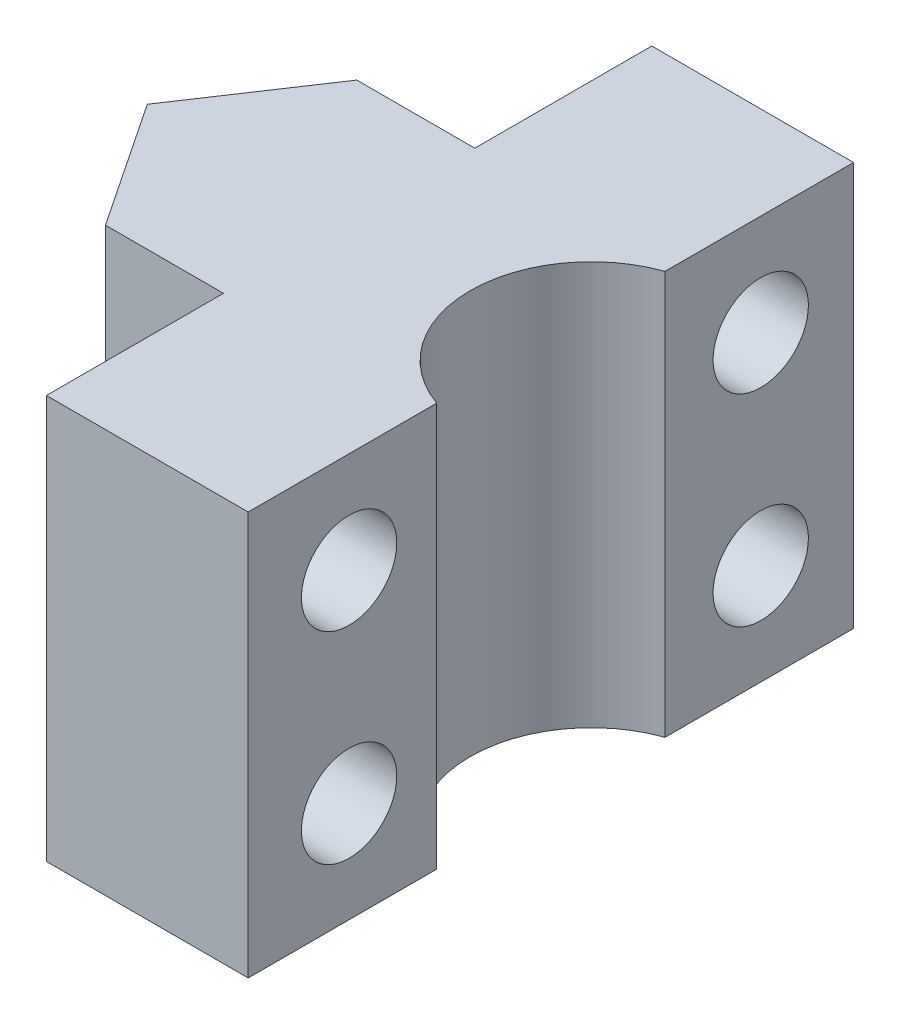
SolidWorks part; units mm, degrees
ref_plane "Front Plane" through (0, 0, 0) normal (0, 0, 1) x (1, 0, 0)
ref_plane "Top Plane" through (0, 0, 0) normal (0, 1, 0) x (1, 0, 0)
ref_plane "Right Plane" through (0, 0, 0) normal (1, 0, 0) x (0, 0, -1)
sketch "Sketch1" plane through (0, 0, 0) normal (0, 1, 0) x (1, 0, 0)
  line L1 (0, 0) -> (12.7, 0)
  line L2 (0, 0) -> (0, 19.05)
  line L3 (0, 19.05) -> (12.7, 19.05)
  line L4 (12.7, 0) -> (12.7, 19.05)
  dimension "D1" = 12.7
  dimension "D2" = 19.05
extrude "Boss-Extrude1" add sketch "Sketch1" along normal blind 12.7
sketch "Sketch4" plane through (0, 12.7, 0) normal (0, 1, 0) x (1, 0, 0)
  line L0 (0, 9.525) -> (6.35, 19.05)
  line L1 (0, 19.05) -> (0, 0) construction
  line L2 (12.7, 19.05) -> (0, 19.05) construction
  line L3 (6.35, 19.05) -> (0, 19.05)
  line L4 (0, 19.05) -> (0, 0)
  line L5 (0, 0) -> (6.35, 0)
  line L6 (0, 0) -> (12.7, 0) construction
  line L7 (6.35, 0) -> (0, 9.525)
  line L8 (12.7, 0) -> (12.7, 19.05) construction
  circle A0 centre (13.97, 9.525) radius 3.81
  line M1 (0, 19.05) -> (0, 0)
  line M2 (0, 0) -> (12.7, 0)
  line M3 (12.7, 0) -> (12.7, 19.05)
  line M4 (12.7, 19.05) -> (0, 19.05)
  dimension "D1" = 7.62
  dimension "D2" = 1.27
extrude "Cut-Extrude2" cut sketch "Sketch4" against normal blind 12.7 contours L0 M1 M4 | L7 M2 M1 | A0 M3
sketch "Sketch5" plane through (12.7, 0, 0) normal (1, 0, 0) x (0, 0, -1)
  line L0 (0, 12.7) -> (5.9329, 12.7) construction
  line L1 (0, 12.7) -> (0, 0) construction
  circle A0 centre (3.175, 9.525) radius 1.5
  circle A1 centre (16.129, 9.525) radius 1.5
  circle A2 centre (16.129, 3.175) radius 1.5
  circle A3 centre (3.175, 3.175) radius 1.5
  dimension "D1" = 3
  dimension "D2" = 3.175
  dimension "D3" = 3.175
  dimension "D4" = 2
  dimension "D5" = 2
extrude "Cut-Extrude3" cut sketch "Sketch5" against normal blind 12.7
sketch "Sketch6" plane through (0, 0, 0) normal (0, -1, 0) x (1, 0, 0)
  line L0 (6.35, 0) -> (6.35, -5.5703)
  line L2 (2.6365, -5.5703) -> (6.35, 0)
  line L3 (2.6365, -5.5703) -> (6.35, -5.5703)
  line L4 (6.35, 0) -> (0, -9.525) construction
extrude "Cut-Extrude4" cut sketch "Sketch6" against normal blind 12.7
ref_plane "Plane1" through (0, 0, -9.525) normal (0, 0, -1) x (0, 1, 0)
mirror "Mirror1" about plane through (0, 0, -9.525) normal (0, 0, -1) of "Cut-Extrude4"
